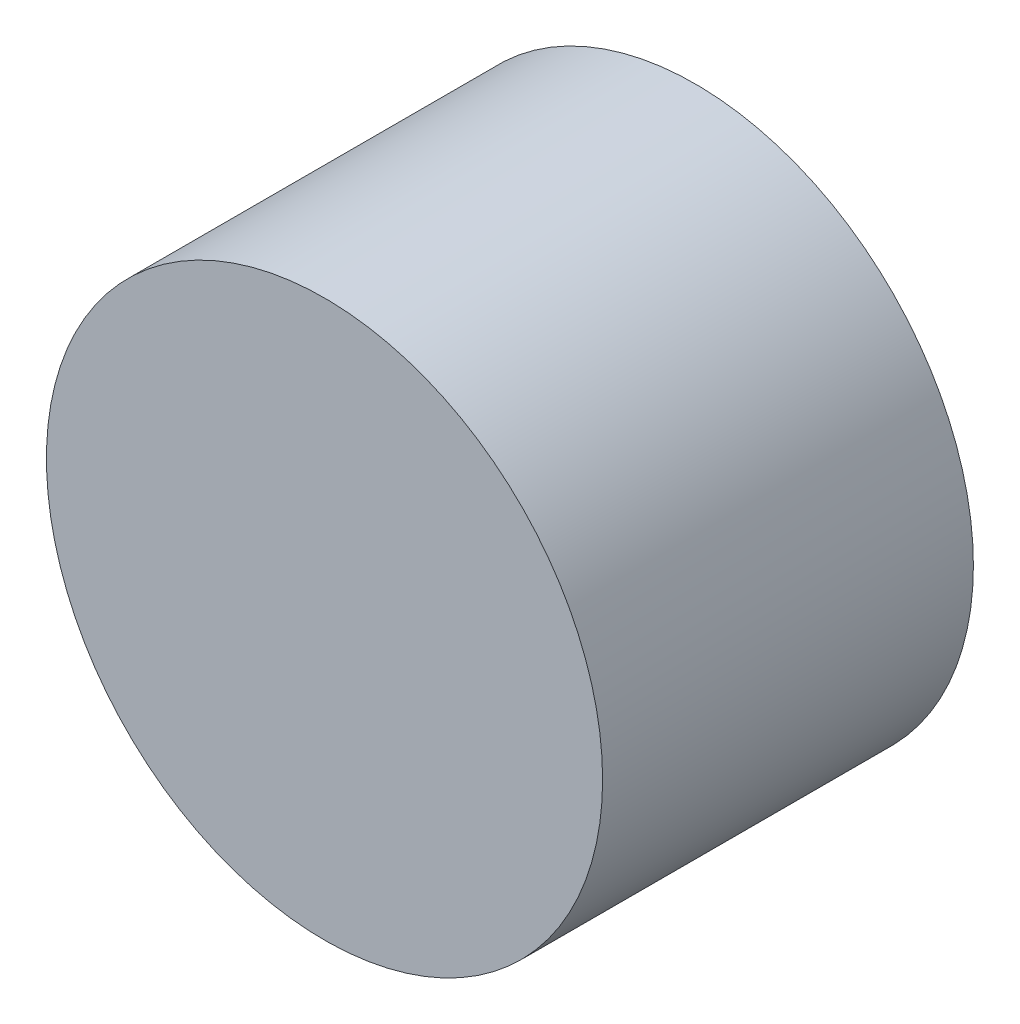
SolidWorks part; units mm, degrees
ref_plane "前视基准面" through (0, 0, 0) normal (0, 0, 1) x (1, 0, 0)
ref_plane "上视基准面" through (0, 0, 0) normal (0, 1, 0) x (1, 0, 0)
ref_plane "右视基准面" through (0, 0, 0) normal (1, 0, 0) x (0, 0, -1)
sketch "草图1" plane through (0, 0, 0) normal (0, 0, 1) x (1, 0, 0)
  circle A0 centre (0, 0) radius 1.5
extrude "凸台-拉伸1" add sketch "草图1" along normal blind 2
